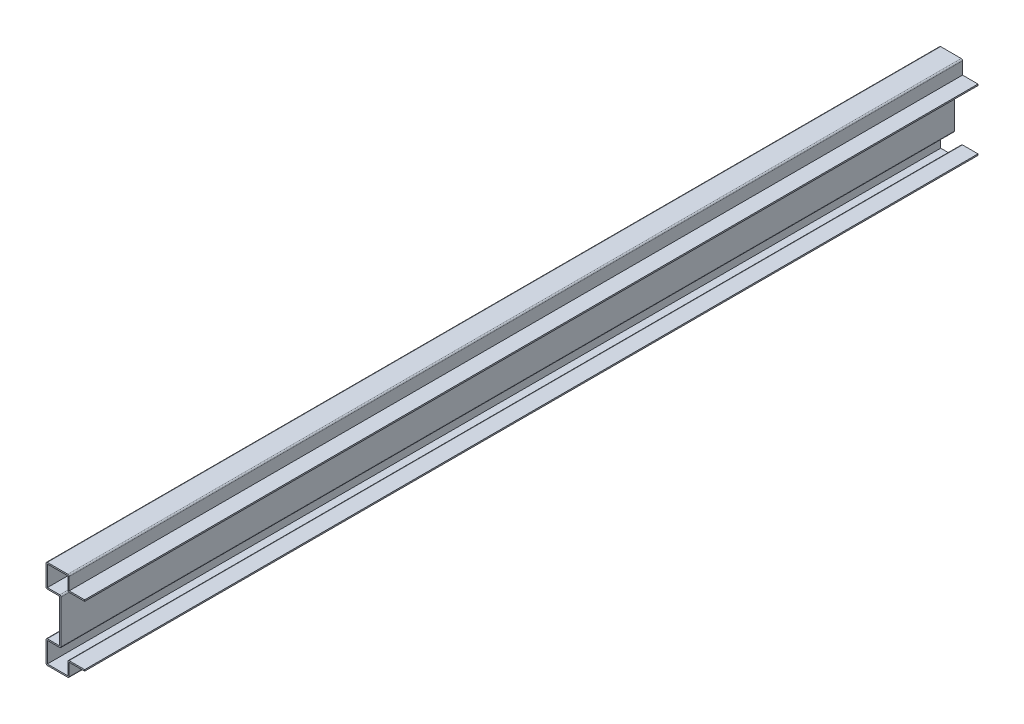
SolidWorks part; units mm, degrees
ref_plane "Front Plane" through (0, 0, 0) normal (0, 0, 1) x (1, 0, 0)
ref_plane "Top Plane" through (0, 0, 0) normal (0, 1, 0) x (1, 0, 0)
ref_plane "Right Plane" through (0, 0, 0) normal (1, 0, 0) x (0, 0, -1)
sketch "Sketch1" plane through (0, 0, 0) normal (0, 0, 1) x (1, 0, 0)
  line L0 (0, 12.7) -> (-14.2875, 12.7)
  line L1 (-14.2875, 12.7) -> (-14.2875, 0)
  line L2 (-14.2875, 0) -> (-35.7187, 0)
  line L3 (-35.7187, 0) -> (-35.7187, 21.4312)
  line L4 (-35.7187, 21.4312) -> (-23.0187, 21.4312)
  line L5 (-23.0187, 21.4312) -> (-23.0187, 61.1187)
  line L6 (-23.0187, 41.275) -> (0, 41.275) construction
  line L7 (0, 41.275) -> (0, 0) construction
  line L8 (-35.7187, 61.1187) -> (-23.0187, 61.1187)
  line L9 (-35.7187, 82.55) -> (-35.7187, 61.1187)
  line L10 (-14.2875, 82.55) -> (-35.7187, 82.55)
  line L11 (-14.2875, 69.85) -> (-14.2875, 82.55)
  line L12 (0, 69.85) -> (-14.2875, 69.85)
  line L13 (0, 68.58) -> (-15.5575, 68.58)
  line L14 (-15.5575, 68.58) -> (-15.5575, 81.28)
  line L15 (-15.5575, 81.28) -> (-34.4487, 81.28)
  line L16 (-34.4487, 81.28) -> (-34.4487, 62.3887)
  line L17 (-34.4487, 62.3887) -> (-21.7487, 62.3887)
  line L18 (-21.7487, 20.1612) -> (-21.7487, 62.3887)
  line L19 (-34.4487, 20.1612) -> (-21.7487, 20.1612)
  line L20 (-34.4487, 1.27) -> (-34.4487, 20.1612)
  line L21 (-15.5575, 1.27) -> (-34.4487, 1.27)
  line L22 (-15.5575, 13.97) -> (-15.5575, 1.27)
  line L23 (0, 13.97) -> (-15.5575, 13.97)
  line L24 (0, 69.85) -> (0, 68.58)
  line L25 (0, 12.7) -> (0, 13.97)
  point P3 (0, 12.7)
  dimension "D1" = 12.7
  dimension "D2" = 21.4312
  dimension "D3" = 14.2875
  dimension "D4" = 12.7
  dimension "D5" = 21.4312
  dimension "D6" = 39.6875
  dimension "D7" = 1.27
extrude "Boss-Extrude1" add sketch "Sketch1" against normal blind 825.5
fillet "Fillet1" radius 1.27 10 edges at (-21.7487, 20.1612, -412.75) (-15.5575, 13.97, -412.75) (-14.2875, 0, -412.75) (-35.7187, 0, -412.75) (-35.7187, 21.4312, -412.75) (-21.7487, 62.3887, -412.75) (-35.7187, 61.1187, -412.75) (-35.7187, 82.55, -412.75) (-15.5575, 68.58, -412.75) (-14.2875, 82.55, -412.75)
